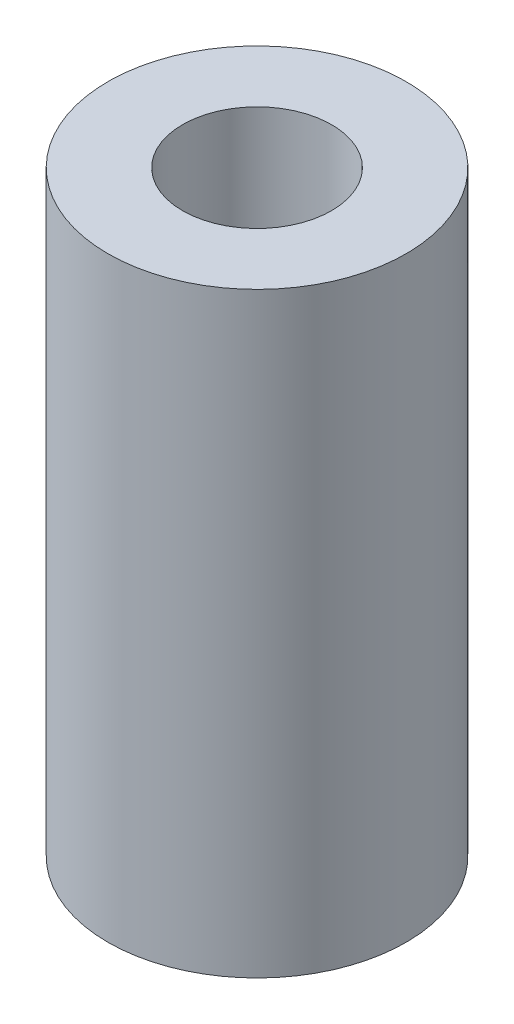
SolidWorks part; units mm, degrees
ref_plane "Front Plane" through (0, 0, 0) normal (0, 0, 1) x (1, 0, 0)
ref_plane "Top Plane" through (0, 0, 0) normal (0, 1, 0) x (1, 0, 0)
ref_plane "Right Plane" through (0, 0, 0) normal (1, 0, 0) x (0, 0, -1)
sketch "Sketch1" plane through (0, 0, 0) normal (0, 1, 0) x (1, 0, 0)
  circle A0 centre (0, 0) radius 6.35
  circle A1 centre (0, 0) radius 3.175
extrude "Boss-Extrude1" add sketch "Sketch1" along normal blind 25.4
